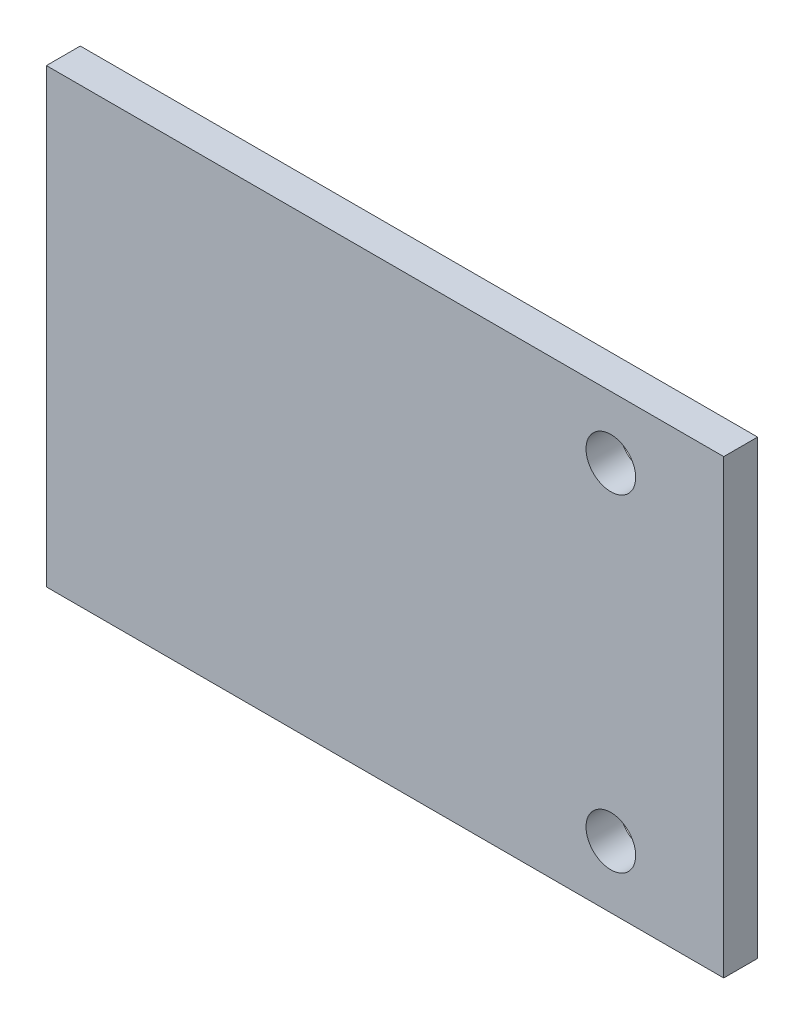
SolidWorks part; units mm, degrees
ref_plane "正面" through (0, 0, 0) normal (0, 0, 1) x (1, 0, 0)
ref_plane "平面" through (0, 0, 0) normal (0, 1, 0) x (1, 0, 0)
ref_plane "右側面" through (0, 0, 0) normal (1, 0, 0) x (0, 0, -1)
sketch "ｽｹｯﾁ1" plane through (0, 0, 0) normal (0, 0, 1) x (1, 0, 0)
  line L1 (-30, 20) -> (30, 20)
  line L2 (-30, 20) -> (-30, -20)
  line L3 (-30, -20) -> (30, -20)
  line L4 (30, 20) -> (30, -20)
  line L5 (-30, 20) -> (30, -20) construction
  line L6 (-30, -20) -> (30, 20) construction
  point P0 (0, 0)
  dimension "D1" = 40
  dimension "D2" = 60
extrude "ﾎﾞｽ - 押し出し1" add sketch "ｽｹｯﾁ1" along normal blind 3
sketch "ｽｹｯﾁ2" plane through (0, 0, 3) normal (0, 0, 1) x (1, 0, 0)
  line L1 (30, 20) -> (20, 20)
  line L2 (30, 20) -> (30, 14.5)
  line L3 (30, 14.5) -> (20, 14.5)
  line L4 (20, 20) -> (20, 14.5)
  line L5 (30, -20) -> (20, -20)
  line L6 (30, -20) -> (30, -14.5)
  line L7 (30, -14.5) -> (20, -14.5)
  line L8 (20, -20) -> (20, -14.5)
  circle A0 centre (20, 14.5) radius 2.2
  circle A1 centre (20, -14.5) radius 2.2
  dimension "D5" = 4.4
  dimension "D6" = 4.4
  dimension "D1" = 10
  dimension "D2" = 10
  dimension "D3" = 5.5
  dimension "D4" = 5.5
extrude "ｶｯﾄ - 押し出し1" cut sketch "ｽｹｯﾁ2" against normal blind 3 contours L4 A0 L3 | L3 A0 L4 | L7 A1 L8 | L8 A1 L7
